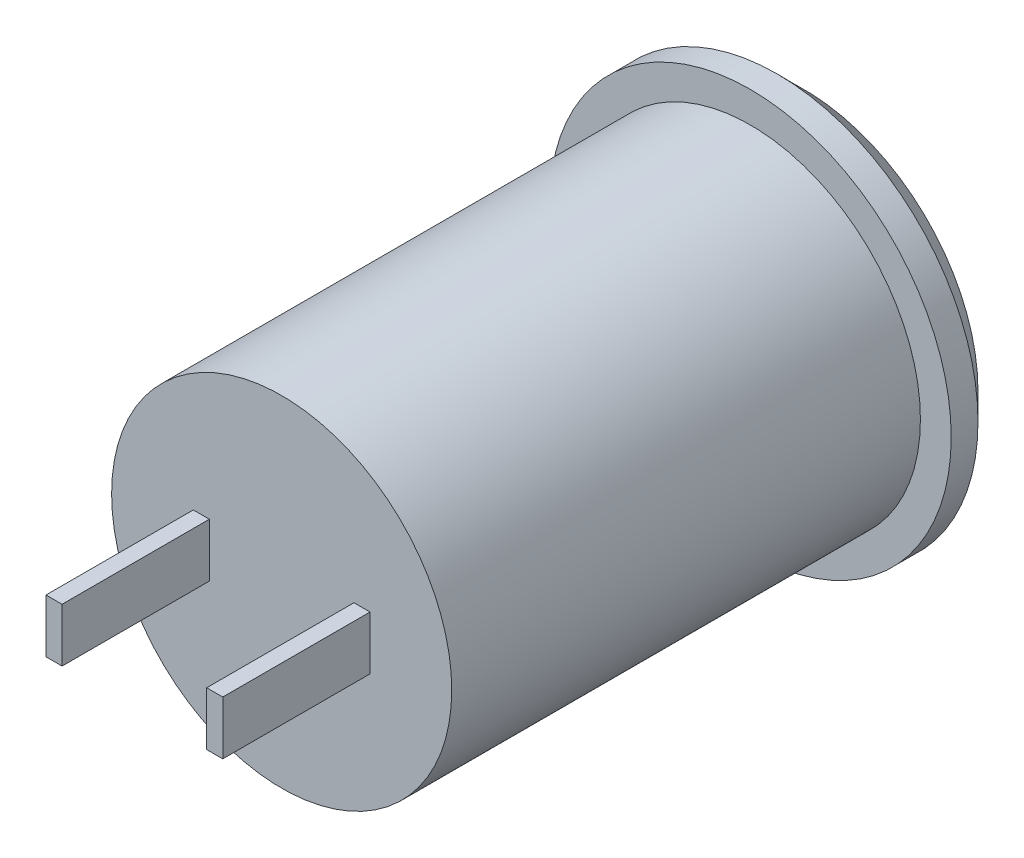
SolidWorks part; units mm, degrees
ref_plane "Front Plane" through (0, 0, 0) normal (0, 0, 1) x (1, 0, 0)
ref_plane "Top Plane" through (0, 0, 0) normal (0, 1, 0) x (1, 0, 0)
ref_plane "Right Plane" through (0, 0, 0) normal (1, 0, 0) x (0, 0, -1)
sketch "Sketch1" plane through (0, 0, 0) normal (0, 1, 0) x (1, 0, 0)
  line L0 (0, 0) -> (6.35, 0)
  line L1 (6.35, 0) -> (6.35, 17.5)
  line L2 (6.35, 17.5) -> (7.5, 17.5)
  line L3 (7.5, 17.5) -> (7.5, 18.5)
  line L4 (7.5, 18.5) -> (6.5, 19.5)
  line L5 (6.5, 19.5) -> (0, 19.5)
  line L6 (0, 19.5) -> (0, 0)
  line L7 (-7.5, 18.5) -> (-6.5, 19.5) construction
  line L8 (-7.5, 17.5) -> (-7.5, 18.5) construction
  line L9 (-6.35, 17.5) -> (-7.5, 17.5) construction
  line L10 (-6.35, 0) -> (-6.35, 17.5) construction
  line L11 (-6.5, 19.5) -> (-7.5, 19.5) construction
  line L12 (-7.5, 19.5) -> (-7.5, 18.5) construction
  line L13 (7.5, 18.5) -> (-7.5, 18.5) construction
  line L14 (-6.5, 19.5) -> (0, 19.5) construction
  line L15 (-6.35, 0) -> (0, 0) construction
  dimension "D1" = 15
  dimension "D2" = 2
  dimension "D3" = 17.5
  dimension "D4" = 45
  dimension "D5" = 12.7
revolve "Revolve2" add sketch "Sketch1" angle 360 about L6
sketch "Sketch2" plane through (0, 0, -19.5) normal (0, 0, -1) x (-1, 0, 0)
  point P0 (0, 0)
hole_wizard "3/8 (0.375) Diameter Hole1" positions "Sketch4" profile "Sketch5" hole size "3/8" standard "ANSI Inch"
sketch "Sketch4" plane through (0, 0, -19.5) normal (0, 0, -1) x (-1, 0, 0)
  point P0 (0, 0)
sketch "Sketch5" plane through (0, 0, -19.5) normal (1, 0, 0) x (0, 1, 0)
  line L0 (0, 0) -> (0, 8.8616)
  line L1 (0, 8.8616) -> (4.7625, 6)
  line L2 (4.7625, 6) -> (4.7625, 0)
  line L5 (4.7625, 0) -> (0, 0)
  line L10 (0, 8.8616) -> (-4.7625, 6) construction
  line L11 (0, -6.35) -> (0, 107.95) construction
  dimension "Hole Dia." = 9.525
  dimension "Hole Depth" = 6
  dimension "Drill Angle" = 118
sketch "Sketch6" plane through (0, 0, 0) normal (0, 0, 1) x (1, 0, 0)
  line L0 (0, 0) -> (-12.4708, 0) construction
  line L1 (-3.3, 1) -> (-2.7, 1)
  line L2 (-3.3, 1) -> (-3.3, -1)
  line L3 (-3.3, -1) -> (-2.7, -1)
  line L4 (-2.7, 1) -> (-2.7, -1)
  line L5 (-3, 1) -> (-3, -1) construction
  point P7 (-2.7, 0)
  dimension "D1" = 0.6
  dimension "D2" = 2
  dimension "D3" = 3
extrude "Boss-Extrude1" add sketch "Sketch6" along normal blind 5.5
mirror "Mirror1" about plane through (0, 0, 0) normal (1, 0, 0) of "Boss-Extrude1"
